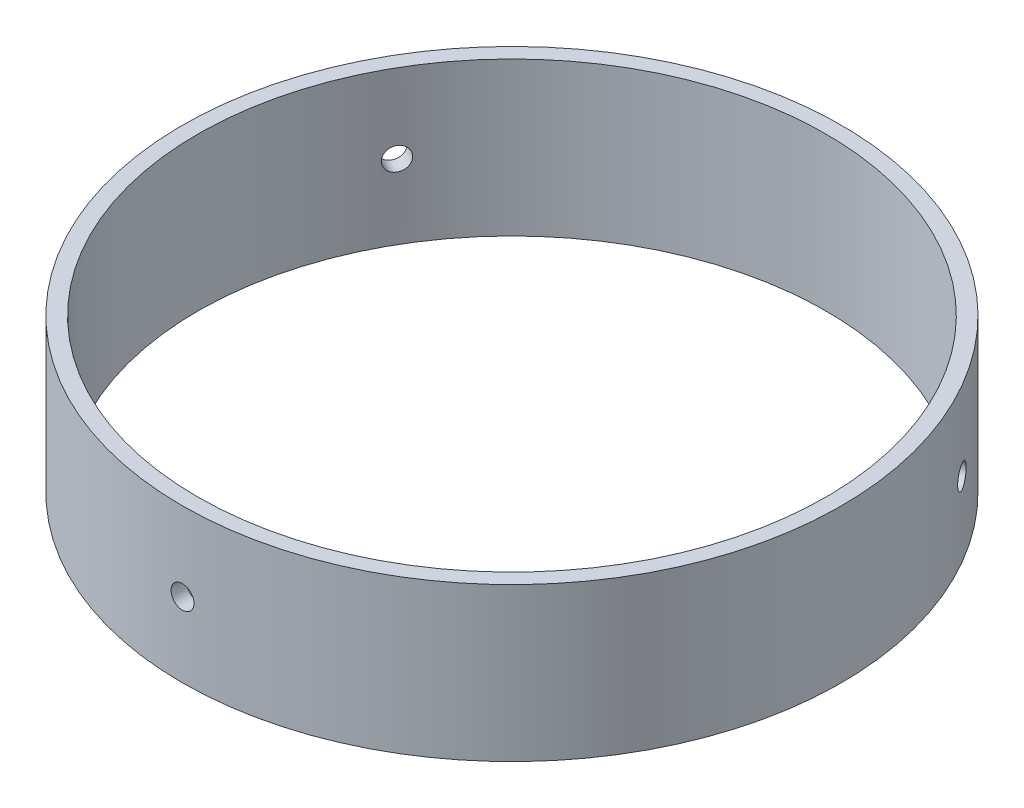
SolidWorks part; units mm, degrees
ref_plane "Front Plane" through (0, 0, 0) normal (0, 0, 1) x (1, 0, 0)
ref_plane "Top Plane" through (0, 0, 0) normal (0, 1, 0) x (1, 0, 0)
ref_plane "Right Plane" through (0, 0, 0) normal (1, 0, 0) x (0, 0, -1)
sketch "Sketch1" plane through (0, 0, 0) normal (0, 1, 0) x (1, 0, 0)
  circle A0 centre (0, 0) radius 52.07
  circle A1 centre (0, 0) radius 54.61
  dimension "D1" = 104.14
  dimension "D2" = 2.54
extrude "Boss-Extrude1" add sketch "Sketch1" along normal blind 25.4
sketch "Sketch3" plane through (0, 0, 0) normal (0, 0, 1) x (1, 0, 0)
  circle A0 centre (0, 12.329) radius 1.905
  dimension "D1" = 3.81
extrude "Cut-Extrude1" cut sketch "Sketch3" along normal through all
pattern_circular "CirPattern1" count 3 over 360 about axis through (0, 25.4, 0) along (0, 1, 0) of "Cut-Extrude1"
